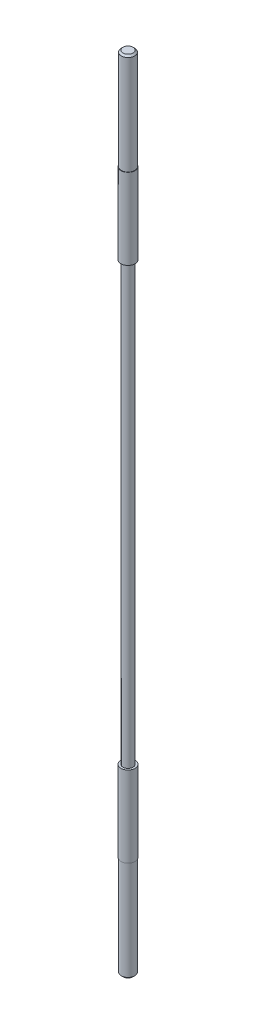
SolidWorks part; units mm, degrees
ref_plane "Vorne" through (0, 0, 0) normal (0, 0, 1) x (1, 0, 0)
ref_plane "Oben" through (0, 0, 0) normal (0, 1, 0) x (1, 0, 0)
ref_plane "Rechts" through (0, 0, 0) normal (1, 0, 0) x (0, 0, -1)
sketch "Skizze1" plane through (0, 0, 0) normal (1, 0, 0) x (0, 0, -1)
  line L0 (0, 0) -> (0, 31.4424) construction
  line L1 (0, 0) -> (-2, 0)
  line L2 (-2, 0) -> (-2, -30)
  line L3 (-2, -30) -> (-2.1, -30)
  line L4 (-2.1, -30) -> (-2.1, -54)
  line L5 (-2.1, -54) -> (-1.5, -54)
  line L6 (-1.5, -54) -> (-1.5, -184)
  line L7 (-1.5, -184) -> (-2.1, -184)
  line L8 (-2.1, -184) -> (-2.1, -208)
  line L9 (-2.1, -208) -> (-2, -208)
  line L10 (-2, -208) -> (-2, -238)
  line L11 (-2, -238) -> (0, -238)
  line L12 (0, -238) -> (0, 0)
  dimension "D1" = 30
  dimension "D2" = 54
  dimension "D3" = 130
  dimension "D4" = 4
  dimension "D5" = 0.1
  dimension "D6" = 3
revolve "Rotation1" add sketch "Skizze1" angle 360 about L0
chamfer "Fase1" distance 0.5 angle 45 2 edges at (0, -238, -2) (0, 0, -2)
